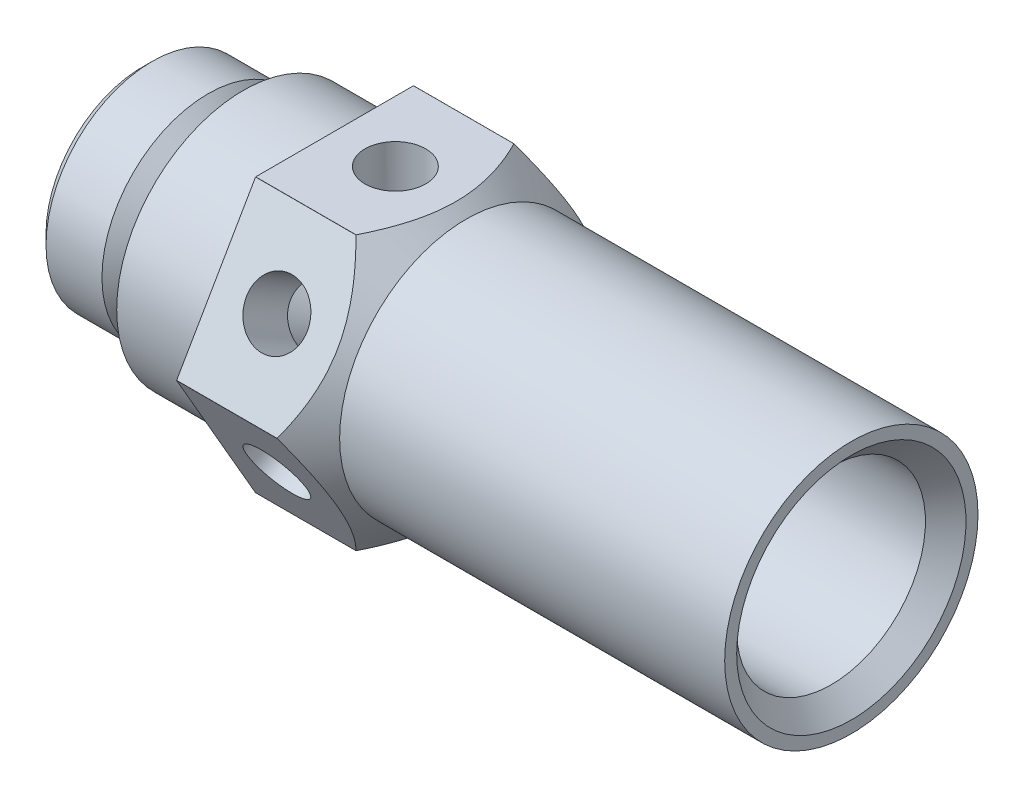
SolidWorks part; units mm, degrees
ref_plane "Płaszczyzna przednia" through (0, 0, 0) normal (0, 0, 1) x (1, 0, 0)
ref_plane "Płaszczyzna górna" through (0, 0, 0) normal (0, 1, 0) x (1, 0, 0)
ref_plane "Płaszczyzna prawa" through (0, 0, 0) normal (1, 0, 0) x (0, 0, -1)
sketch "Szkic1" plane through (0, 0, 0) normal (0, 0, 1) x (1, 0, 0)
  line L0 (0, 0) -> (72.3643, 0) construction
  line L1 (0, -4) -> (0, -9.4775)
  line L2 (0, -9.4775) -> (1, -10.4775)
  line L3 (1, -10.4775) -> (6.5225, -10.4775)
  line L4 (6.5225, -10.4775) -> (8, -9)
  line L5 (8, -9) -> (10, -9)
  line L6 (10, -9) -> (10, -11.1)
  line L7 (10, -12.5) -> (19, -12.5)
  line L8 (19, -12.5) -> (19, -15.585)
  line L9 (19, -15.585) -> (28.915, -15.585)
  line L10 (28.915, -15.585) -> (32, -12.5)
  line L11 (32, -12.5) -> (70, -12.5)
  line L12 (70, -12.5) -> (70, -11.3155)
  line L13 (70, -11.3155) -> (68, -9.3155)
  line L14 (68, -9.3155) -> (54, -9.3155)
  line L15 (54, -9.3155) -> (53, -10.5)
  line L16 (53, -10.5) -> (50, -10.5)
  line L17 (50, -10.5) -> (50, -8.5)
  line L20 (19, -8.1) -> (22, -5)
  line L24 (10, -12.1) -> (10.4899, -11.5)
  line L25 (10.4899, -11.5) -> (10, -11.1)
  line L26 (10, -12.1) -> (10, -12.5)
  line L27 (0, -4) -> (19, -4)
  line L28 (22, -5) -> (19, -5)
  line L29 (19, -5) -> (19, -4)
  line L31 (50, -8.5) -> (19, -8.5)
  line L32 (19, -8.1) -> (19, -8.5)
  dimension "D1" = 70
  dimension "D2" = 38
  dimension "D3" = 31.17
  dimension "D4" = 25
  dimension "D5" = 20.955
  dimension "D6" = 8
  dimension "D7" = 1
  dimension "D8" = 135
  dimension "D9" = 18.631
  dimension "D10" = 3
  dimension "D11" = 4
  dimension "D12" = 2
  dimension "D13" = 45
  dimension "D14" = 18
  dimension "D15" = 2
  dimension "D16" = 19
  dimension "D17" = 0.4
  dimension "D18" = 17
  dimension "D19" = 0.4
  dimension "D20" = 25
  dimension "D21" = 10
  dimension "D22" = 3
  dimension "D23" = 23
  dimension "D24" = 1
  dimension "D25" = 90
  dimension "D26" = 135
  dimension "D27" = 21
  dimension "D28" = 20
  dimension "D29" = 45
  dimension "D30" = 10
revolve "Obrót1" add sketch "Szkic1" angle 360 about L0
cosmetic thread "Oznaczenie gwintu1" parameters "D2"=18.631
cosmetic thread "Oznaczenie gwintu2" parameters "D2"=20.955
sketch "Szkic2" plane through (19, 0, 0) normal (-1, 0, 0) x (0, 0, 1)
  line L0 (-7.7873, 13.5) -> (7.7873, 13.5)
  circle A0 centre (0, 0) radius 15.585 construction
  dimension "D1" = 13.5
extrude "Wytnij-wyciągnięcie1" cut sketch "Szkic2" against normal through all and the other way through all
sketch "Szkic3" plane through (0, 13.5, 0) normal (0, 1, 0) x (1, 0, 0)
  line L0 (19, -7.7873) -> (19, 7.7873) construction
  circle A0 centre (25, 0) radius 3
  dimension "D1" = 6
  dimension "D2" = 6
extrude "Wytnij-wyciągnięcie2" cut sketch "Szkic3" against normal blind 12
pattern_circular "Szyk kołowy1" count 6 over 360 about axis through (0, 0, 0) along (-1, 0, 0) of "Wytnij-wyciągnięcie2", "Wytnij-wyciągnięcie1"
